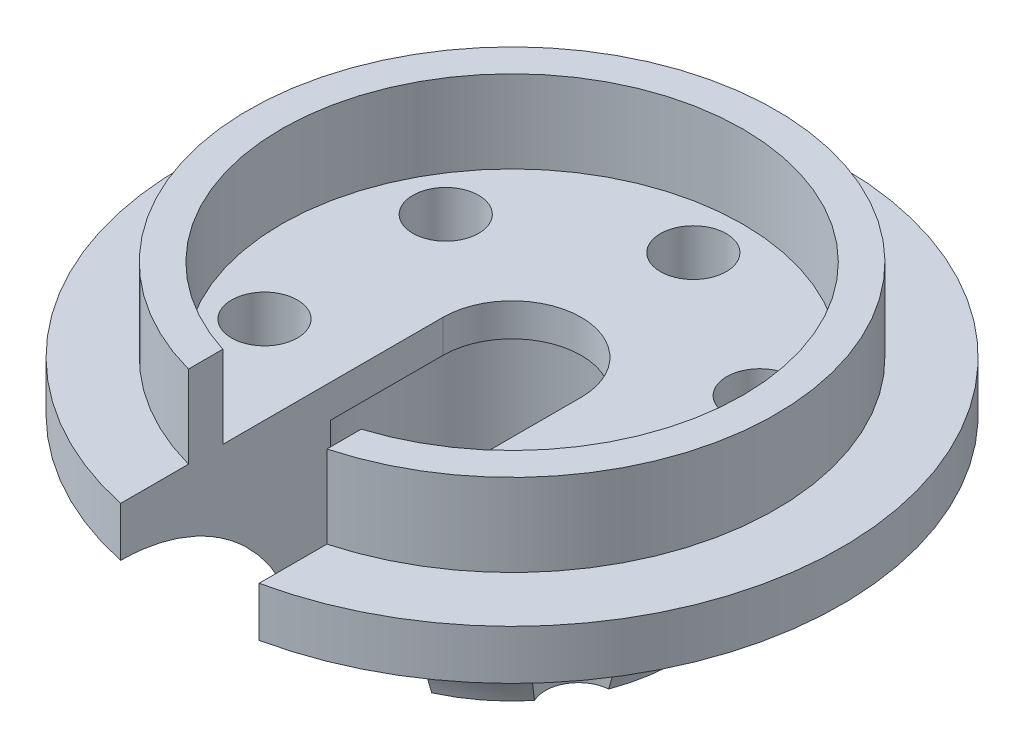
SolidWorks part; units mm, degrees
ref_plane "Front Plane" through (0, 0, 0) normal (0, 0, 1) x (1, 0, 0)
ref_plane "Top Plane" through (0, 0, 0) normal (0, 1, 0) x (1, 0, 0)
ref_plane "Right Plane" through (0, 0, 0) normal (1, 0, 0) x (0, 0, -1)
sketch "Sketch1" plane through (0, 0, 0) normal (0, 0, 1) x (1, 0, 0)
  line L0 (0, 0) -> (0, 8)
  line L1 (0, 8) -> (-8, 8)
  line L2 (-8, 8) -> (-8, 5.5)
  line L3 (-8, 5.5) -> (-10, 5.5)
  line L4 (-10, 5.5) -> (-10, 4)
  line L5 (-5, 0) -> (0, 0)
  line L6 (-10, 4) -> (-2.8415, 4) construction
  arc A0 (-10, 4) -> (-5, 0) centre (-10, -1.125) cw
  dimension "D1" = 8
  dimension "D2" = 8
  dimension "D3" = 2
  dimension "D4" = 2.5
  dimension "D5" = 5
  dimension "D6" = 1.5
revolve "Revolve1" add sketch "Sketch1" angle 360 about L0
sketch "Sketch2" plane through (0, 8, 0) normal (0, 1, 0) x (1, 0, 0)
  circle A0 centre (0, 0) radius 7
  circle A1 centre (0, 0) radius 8 construction
  dimension "D1" = 1
extrude "Cut-Extrude1" cut sketch "Sketch2" against normal blind 2.5
sketch "Sketch3" plane through (0, 5.5, 0) normal (0, 1, 0) x (1, 0, 0)
  circle A0 centre (0, 0) radius 2.1
  dimension "D1" = 4.2
extrude "Cut-Extrude2" cut sketch "Sketch3" against normal through all
sketch "Sketch4" plane through (0, 0, 0) normal (0, -1, 0) x (1, 0, 0)
  circle A0 centre (0, 0) radius 4
  circle A1 centre (0, 0) radius 5 construction
  dimension "D1" = 1
extrude "Cut-Extrude3" cut sketch "Sketch4" against normal offset from surface (4.5 mm away) 1 up to face at (0, 5.5, 2.1)
sketch3d "3DSketch1" plane through (0, 0, 0) normal (0, 0, 1) x (1, 0, 0)
sketch "Sketch5" plane through (0, 0, 10) normal (0, 0, 1) x (1, 0, 0)
  line L0 (2.1, 5.5) -> (-2.1, 5.5) construction
  line L1 (2.1, 5.5) -> (-2.1, 5.5)
  line L2 (-2.1, 5.5) -> (-2.1, 0)
  line L3 (-2.1, 0) -> (2.1, 0)
  line L4 (2.1, 0) -> (2.1, 5.5)
  line L5 (-2.1, 5.5) -> (-2.1, 8.9492)
  line L6 (-2.1, 8.9492) -> (2.1, 8.9492)
  line L7 (2.1, 8.9492) -> (2.1, 5.5)
  dimension "D1" = 3.4492
extrude "Cut-Extrude4" cut sketch "Sketch5" against normal up to surface (10 mm away) contours L3 L4 L1 L2 | L7 L6 L5 L1 up to plane "Front Plane"
sketch "Sketch6" plane through (0, 5.5, 0) normal (0, 1, 0) x (1, 0, 0)
  line L0 (0, 7) -> (0, -7.9941) construction
  arc A0 (2.1, -6.6776) -> (-2.1, -6.6776) centre (0, 0) ccw construction
  circle A1 centre (0, 5.5) radius 1
  circle A2 centre (0, 0) radius 5.5 construction
  circle A3 centre (4.7631, 2.75) radius 1
  circle A4 centre (4.7631, -2.75) radius 1
  circle A5 centre (0, -5.5) radius 1
  circle A6 centre (-4.7631, -2.75) radius 1
  circle A7 centre (-4.7631, 2.75) radius 1
  point P12 (0, 0)
  point P23 (0, 0)
  dimension "D1" = 2
  dimension "D2" = 1.5
  dimension "D3" = 6
extrude "Cut-Extrude5" cut sketch "Sketch6" against normal through all contours A1 | A7 | A6 | A5 | A4 | A3
